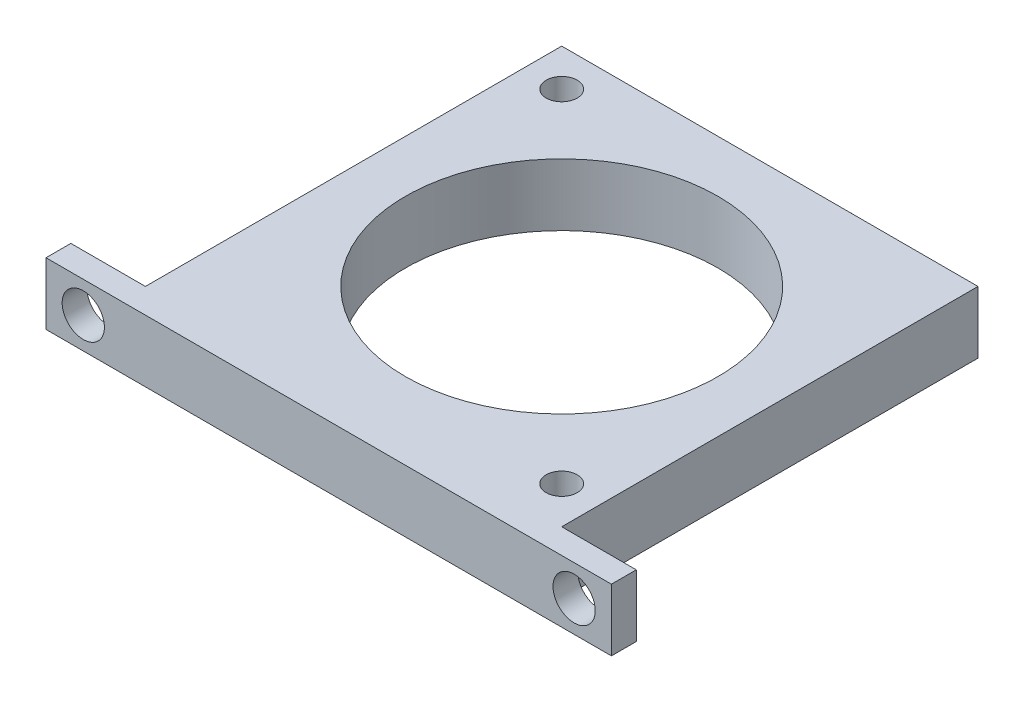
SolidWorks part; units mm, degrees
ref_plane "Front Plane" through (0, 0, 0) normal (0, 0, 1) x (1, 0, 0)
ref_plane "Top Plane" through (0, 0, 0) normal (0, 1, 0) x (1, 0, 0)
ref_plane "Right Plane" through (0, 0, 0) normal (1, 0, 0) x (0, 0, -1)
sketch "Sketch1" plane through (0, 0, 0) normal (0, 1, 0) x (1, 0, 0)
  line L1 (-16.75, 16.75) -> (16.75, 16.75)
  line L2 (-16.75, 16.75) -> (-16.75, -16.75)
  line L3 (-16.75, -16.75) -> (16.75, -16.75)
  line L4 (16.75, 16.75) -> (16.75, -16.75)
  line L5 (-16.75, 16.75) -> (16.75, -16.75) construction
  line L6 (-16.75, -16.75) -> (16.75, 16.75) construction
  point P0 (0, 0)
  dimension "D1" = 33.5
  dimension "D2" = 33.5
extrude "Boss-Extrude1" add sketch "Sketch1" along normal blind 70
hole_wizard "M3x0.5 Tapped Hole1" positions "3DSketch3" profile "Sketch5" tap size "M3x0.5" standard "ANSI Metric"
sketch3d "3DSketch3"
  line L0 (-16.75, 70, -16.75) -> (-16.75, 70, 16.75) construction
  line L1 (-16.75, 70, 16.75) -> (16.75, 70, 16.75) construction
  line L2 (16.75, 70, -16.75) -> (-16.75, 70, -16.75) construction
  line L3 (16.75, 70, 16.75) -> (16.75, 70, -16.75) construction
  point P0 (13.75, 70, 13.75)
  point P2 (-13.75, 70, -13.75)
  dimension "D1" = 30.5
  dimension "D2" = 3
  dimension "D3" = 3
  dimension "D4" = 30.5
sketch "Sketch5" plane through (13.75, 70, 13.75) normal (1, 0, 0) x (0, 0, 1)
  line L0 (0, 0) -> (0, 8.3711)
  line L1 (0, 8.3711) -> (1.25, 7.62)
  line L2 (1.25, 7.62) -> (1.25, 0)
  line L5 (1.25, 0) -> (0, 0)
  line L10 (0, 8.3711) -> (-1.25, 7.62) construction
  line L11 (0, -6.35) -> (0, 107.95) construction
  dimension "Tap Drill Dia." = 2.5
  dimension "Tap Drill Depth" = 7.62
  dimension "Drill Angle" = 118
hole_wizard "M3x0.5 Tapped Hole2" positions "3DSketch4" profile "Sketch6" tap size "M3x0.5" standard "ANSI Metric"
sketch3d "3DSketch4"
  line L0 (16.75, 70, 16.75) -> (16.75, 0, 16.75) construction
  line L1 (16.75, 70, -16.75) -> (16.75, 0, -16.75) construction
  line L2 (16.75, 0, 16.75) -> (16.75, 0, -16.75) construction
  point P0 (16.75, 6, 13.75)
  point P2 (16.75, 6, -13.75)
  dimension "D1" = 3
  dimension "D2" = 3
  dimension "D3" = 6
  dimension "D4" = 6
sketch "Sketch6" plane through (16.75, 6, 13.75) normal (0, 1, 0) x (0, 0, -1)
  line L0 (0, 0) -> (0, 8.3711)
  line L1 (0, 8.3711) -> (1.25, 7.62)
  line L2 (1.25, 7.62) -> (1.25, 0)
  line L5 (1.25, 0) -> (0, 0)
  line L10 (0, 8.3711) -> (-1.25, 7.62) construction
  line L11 (0, -6.35) -> (0, 107.95) construction
  dimension "Tap Drill Dia." = 2.5
  dimension "Tap Drill Depth" = 7.62
  dimension "Drill Angle" = 118
sketch "Sketch7" plane through (0, 0, -16.75) normal (0, 0, -1) x (-1, 0, 0)
  line L0 (-16.75, 70) -> (-16.75, 0) construction
  line L1 (-16.75, 11) -> (-22.75, 11)
  line L2 (-16.75, 11) -> (-16.75, 61)
  line L3 (-16.75, 61) -> (-22.75, 61)
  line L4 (-22.75, 11) -> (-22.75, 61)
  line L5 (-16.75, 0) -> (16.75, 0) construction
  dimension "D1" = 6
  dimension "D2" = 11
  dimension "D3" = 50
extrude "Boss-Extrude2" add sketch "Sketch7" against normal blind 3 separate body
sketch "Sketch8" plane through (0, 0, -16.75) normal (0, 0, -1) x (-1, 0, 0)
  line L0 (16.75, 70) -> (16.75, 0) construction
  line L1 (16.75, 61) -> (22.75, 61)
  line L2 (16.75, 61) -> (16.75, 11)
  line L3 (16.75, 11) -> (22.75, 11)
  line L4 (22.75, 61) -> (22.75, 11)
  line L5 (-22.75, 11) -> (-16.75, 11) construction
  line L7 (16.75, 0) -> (-16.75, 0) construction
  dimension "D1" = 6
  dimension "D2" = 0
  dimension "D3" = 50
  dimension "D4" = 11
extrude "Boss-Extrude3" add sketch "Sketch8" against normal blind 3 separate body
hole_wizard "M3 Clearance Hole1" positions "3DSketch5" profile "Sketch10" hole size "M3" standard "ANSI Metric" end condition through all
sketch3d "3DSketch5"
  line L0 (22.75, 11, -16.75) -> (16.75, 11, -16.75) construction
  line L1 (22.75, 61, -16.75) -> (22.75, 11, -16.75) construction
  line L2 (-22.75, 11, -16.75) -> (-22.75, 61, -16.75) construction
  point P0 (19.75, 51, -16.75)
  point P2 (19.75, 26, -16.75)
  point P4 (-19.75, 51, -16.75)
  point P6 (-19.75, 26, -16.75)
  dimension "D1" = 40
  dimension "D2" = 15
  dimension "D3" = 3
  dimension "D4" = 3
  dimension "D5" = 3
  dimension "D6" = 3
  dimension "D7" = 40
  dimension "D8" = 15
sketch "Sketch10" plane through (19.75, 51, -16.75) normal (1, 0, 0) x (0, 1, 0)
  line L0 (0, 0) -> (0, 33.5)
  line L1 (0, 33.5) -> (1.7, 33.5)
  line L2 (1.7, 33.5) -> (1.7, 0)
  line L5 (1.7, 0) -> (0, 0)
  line L11 (0, -6.35) -> (0, 107.95) construction
  dimension "Thru Hole Dia." = 3.4
  dimension "Thru Hole Depth" = 33.5
sketch "Sketch11" plane through (0, 0, 0) normal (0, -1, 0) x (1, 0, 0)
  circle A0 centre (0, 0) radius 12.573
  dimension "D1" = 25.146
extrude "Cut-Extrude1" cut sketch "Sketch11" against normal through all
sketch "Sketch12" plane through (0, 0, 16.75) normal (0, 0, 1) x (1, 0, 0)
  line L0 (16.75, 70) -> (16.75, 0) construction
  line L1 (16.75, 13) -> (-16.75, 13)
  line L2 (16.75, 13) -> (16.75, 58)
  line L3 (16.75, 58) -> (-16.75, 58)
  line L4 (-16.75, 13) -> (-16.75, 58)
  line L5 (-16.75, 70) -> (-16.75, 0) construction
  line L6 (-16.75, 0) -> (16.75, 0) construction
  line L7 (-16.75, 70) -> (16.75, 70) construction
  dimension "D1" = 13
  dimension "D2" = 12
extrude "Cut-Extrude2" cut sketch "Sketch12" against normal blind 32.5
sketch "Sketch13" plane through (0, 0, 16.75) normal (0, 0, 1) x (1, 0, 0)
  line L0 (-16.75, 70) -> (16.75, 70) construction
  line L1 (-22.75, 65) -> (22.75, 65)
  line L2 (-22.75, 65) -> (-22.75, -5.7776)
  line L3 (-22.75, -5.7776) -> (22.75, -5.7776)
  line L4 (22.75, 65) -> (22.75, -5.7776)
  dimension "D1" = 5
extrude "Cut-Extrude3" cut sketch "Sketch13" against normal through all
sketch "Sketch14" plane through (0, 0, 16.75) normal (0, 0, 1) x (1, 0, 0)
  line L0 (16.75, 70) -> (16.75, 65) construction
  line L1 (-22.75, 70) -> (22.75, 70)
  line L2 (-22.75, 70) -> (-22.75, 65)
  line L3 (-22.75, 65) -> (22.75, 65)
  line L4 (22.75, 70) -> (22.75, 65)
  line L5 (-16.75, 70) -> (-16.75, 65) construction
  dimension "D1" = 6
  dimension "D2" = 6
extrude "Boss-Extrude4" add sketch "Sketch14" along normal blind 2
hole_wizard "M3 Clearance Hole2" positions "3DSketch6" profile "Sketch15" hole size "M3" standard "ANSI Metric" end condition through all
sketch3d "3DSketch6"
  line L0 (-16.75, 70, 16.75) -> (-16.75, 65, 16.75) construction
  line L1 (16.75, 70, 16.75) -> (16.75, 65, 16.75) construction
  line L2 (-22.75, 65, 16.75) -> (-16.75, 65, 16.75) construction
  line L3 (16.75, 65, 16.75) -> (22.75, 65, 16.75) construction
  point P0 (-19.75, 67.5, 16.75)
  point P2 (19.75, 67.5, 16.75)
  dimension "D1" = 3
  dimension "D2" = 3
  dimension "D3" = 2.5
  dimension "D4" = 2.5
sketch "Sketch15" plane through (-19.75, 67.5, 16.75) normal (1, 0, 0) x (0, 1, 0)
  line L0 (0, 0) -> (0, 2)
  line L1 (0, 2) -> (1.7, 2)
  line L2 (1.7, 2) -> (1.7, 0)
  line L5 (1.7, 0) -> (0, 0)
  line L11 (0, -6.35) -> (0, 107.95) construction
  dimension "Thru Hole Dia." = 3.4
  dimension "Thru Hole Depth" = 2
